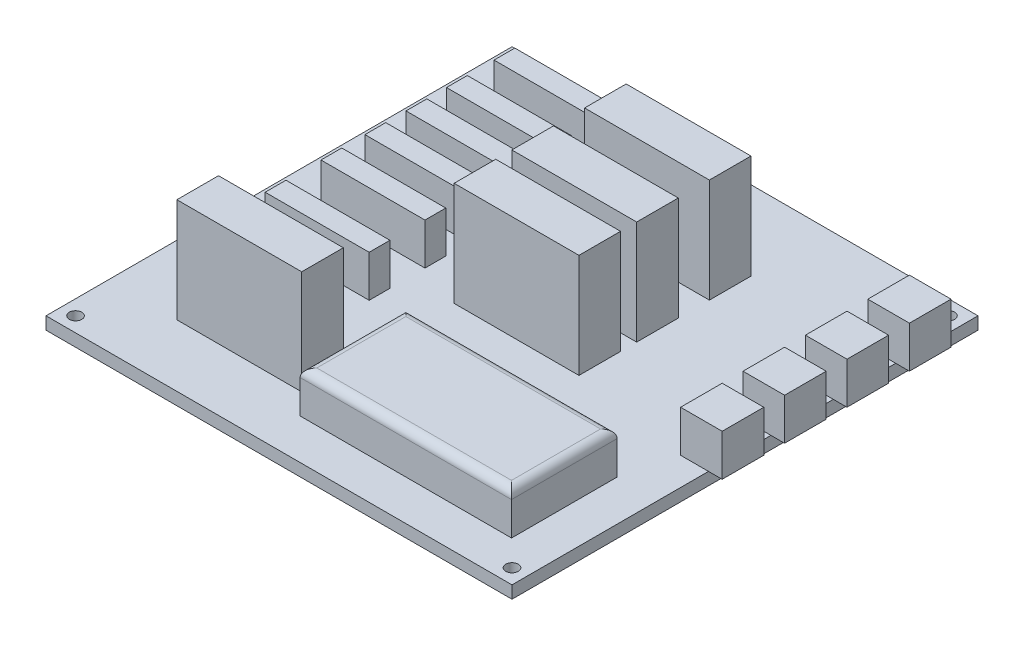
SolidWorks part; units mm, degrees
ref_plane "Face" through (0, 0, 0) normal (0, 0, 1) x (1, 0, 0)
ref_plane "Dessus" through (0, 0, 0) normal (0, 1, 0) x (1, 0, 0)
ref_plane "Droite" through (0, 0, 0) normal (1, 0, 0) x (0, 0, -1)
sketch "Esquisse1" plane through (0, 0, 0) normal (0, 1, 0) x (1, 0, 0)
  line L0 (56, 112) -> (56, 0) construction
  line L1 (0, 0) -> (112, 0)
  line L2 (0, 0) -> (0, 112)
  line L3 (0, 112) -> (112, 112)
  line L4 (112, 0) -> (112, 112)
  line L5 (0, 56) -> (112, 56) construction
  circle A0 centre (3.55, 108.45) radius 1.5
  circle A1 centre (108.45, 108.45) radius 1.5
  circle A2 centre (108.45, 3.55) radius 1.5
  circle A3 centre (3.55, 3.55) radius 1.5
  dimension "D3" = 3
  dimension "D1" = 112
  dimension "D2" = 112
  dimension "D4" = 3.55
  dimension "D5" = 3.55
extrude "Extrusion1" add sketch "Esquisse1" along normal blind 3
sketch "Esquisse2" plane through (0, 3, 0) normal (0, 1, 0) x (1, 0, 0)
  line L1 (51.398, 9.6876) -> (102.198, 9.6876)
  line L2 (51.398, 9.6876) -> (51.398, 35.0876)
  line L3 (51.398, 35.0876) -> (102.198, 35.0876)
  line L4 (102.198, 9.6876) -> (102.198, 35.0876)
  dimension "D1" = 25.4
  dimension "D2" = 50.8
extrude "Extrusion2" add sketch "Esquisse2" along normal blind 10
fillet "Congé1" radius 2 4 edges at (76.798, 13, -35.0876) (102.198, 13, -22.3876) (76.798, 13, -9.6876) (51.398, 13, -22.3876)
sketch "Esquisse3" plane through (0, 3, 0) normal (0, 1, 0) x (1, 0, 0)
  line L0 (105.29, 102.2264) -> (115.29, 102.2264)
  line L1 (115.29, 72.2264) -> (115.29, 62.2264)
  line L2 (105.29, 57.2264) -> (115.29, 57.2264)
  line L3 (105.29, 57.2264) -> (105.29, 47.2264)
  line L4 (105.29, 47.2264) -> (115.29, 47.2264)
  line L5 (115.29, 57.2264) -> (115.29, 47.2264)
  line L13 (105.29, 102.2264) -> (105.29, 92.2264)
  line L14 (105.29, 92.2264) -> (115.29, 92.2264)
  line L15 (115.29, 102.2264) -> (115.29, 92.2264)
  line L16 (105.29, 87.2264) -> (115.29, 87.2264)
  line L17 (105.29, 87.2264) -> (105.29, 77.2264)
  line L18 (105.29, 77.2264) -> (115.29, 77.2264)
  line L19 (115.29, 87.2264) -> (115.29, 77.2264)
  line L20 (105.29, 72.2264) -> (115.29, 72.2264)
  line L21 (105.29, 72.2264) -> (105.29, 62.2264)
  line L22 (105.29, 62.2264) -> (115.29, 62.2264)
  line L25 (115.29, 102.2264) -> (115.29, 62.2264) construction
  dimension "D1" = 10
  dimension "D2" = 10
  dimension "D3" = 5
  dimension "D5" = 10
  dimension "D6" = 10
  dimension "D7" = 5
  dimension "D8" = 5
extrude "Extrusion3" add sketch "Esquisse3" along normal blind 10
sketch "Esquisse4" plane through (0, 3, 0) normal (0, 1, 0) x (1, 0, 0)
  line L0 (46.461, 61.6307) -> (76.461, 61.6307)
  line L1 (46.461, 75.5019) -> (76.461, 75.5019)
  line L2 (46.461, 75.5019) -> (46.461, 65.5019)
  line L3 (46.461, 65.5019) -> (76.461, 65.5019)
  line L4 (76.461, 75.5019) -> (76.461, 65.5019)
  line L5 (16.5699, 24.8897) -> (46.5699, 24.8897)
  line L6 (16.5699, 24.8897) -> (16.5699, 14.8897)
  line L7 (16.5699, 14.8897) -> (46.5699, 14.8897)
  line L8 (46.5699, 24.8897) -> (46.5699, 14.8897)
  line L9 (46.461, 61.6307) -> (46.461, 51.6307)
  line L10 (46.461, 51.6307) -> (76.461, 51.6307)
  line L11 (76.461, 61.6307) -> (76.461, 51.6307)
  line L12 (46.461, 92.9791) -> (76.461, 92.9791)
  line L13 (46.461, 92.9791) -> (46.461, 82.9791)
  line L14 (46.461, 82.9791) -> (76.461, 82.9791)
  line L15 (76.461, 92.9791) -> (76.461, 82.9791)
  dimension "D1" = 10
  dimension "D2" = 30
  dimension "D3" = 10
  dimension "D4" = 30
  dimension "D5" = 10
  dimension "D6" = 30
extrude "Extrusion4" add sketch "Esquisse4" along normal blind 25
sketch "Esquisse6" plane through (0, 3, 0) normal (0, 1, 0) x (1, 0, 0)
  line L0 (35.6118, 75.9109) -> (10.6118, 75.9109)
  line L1 (35.6118, 55.4716) -> (10.6118, 55.4716)
  line L2 (35.6118, 55.4716) -> (35.6118, 60.4716)
  line L3 (35.6118, 60.4716) -> (10.6118, 60.4716)
  line L4 (10.6118, 55.4716) -> (10.6118, 60.4716)
  line L5 (35.6118, 75.9109) -> (35.6118, 80.9109)
  line L6 (35.6118, 80.9109) -> (10.6118, 80.9109)
  line L7 (10.6118, 75.9109) -> (10.6118, 80.9109)
  line L8 (35.6118, 66.0367) -> (10.6118, 66.0367)
  line L9 (35.6118, 66.0367) -> (35.6118, 71.0367)
  line L10 (35.6118, 71.0367) -> (10.6118, 71.0367)
  line L11 (10.6118, 66.0367) -> (10.6118, 71.0367)
  line L12 (35.6118, 42.0564) -> (10.6118, 42.0564)
  line L13 (35.6118, 42.0564) -> (35.6118, 47.0564)
  line L14 (35.6118, 47.0564) -> (10.6118, 47.0564)
  line L15 (10.6118, 42.0564) -> (10.6118, 47.0564)
  line L16 (35.6118, 85.6441) -> (10.6118, 85.6441)
  line L17 (35.6118, 85.6441) -> (35.6118, 90.6441)
  line L18 (35.6118, 90.6441) -> (10.6118, 90.6441)
  line L19 (10.6118, 85.6441) -> (10.6118, 90.6441)
  line L20 (35.6118, 97.07) -> (10.6118, 97.07)
  line L21 (35.6118, 97.07) -> (35.6118, 102.07)
  line L22 (35.6118, 102.07) -> (10.6118, 102.07)
  line L23 (10.6118, 97.07) -> (10.6118, 102.07)
  dimension "D1" = 25
  dimension "D2" = 5
  dimension "D3" = 25
  dimension "D4" = 5
  dimension "D5" = 25
  dimension "D6" = 5
  dimension "D7" = 25
  dimension "D8" = 5
  dimension "D9" = 25
  dimension "D10" = 5
  dimension "D11" = 25
  dimension "D12" = 5
extrude "Extrusion6" add sketch "Esquisse6" along normal blind 10
